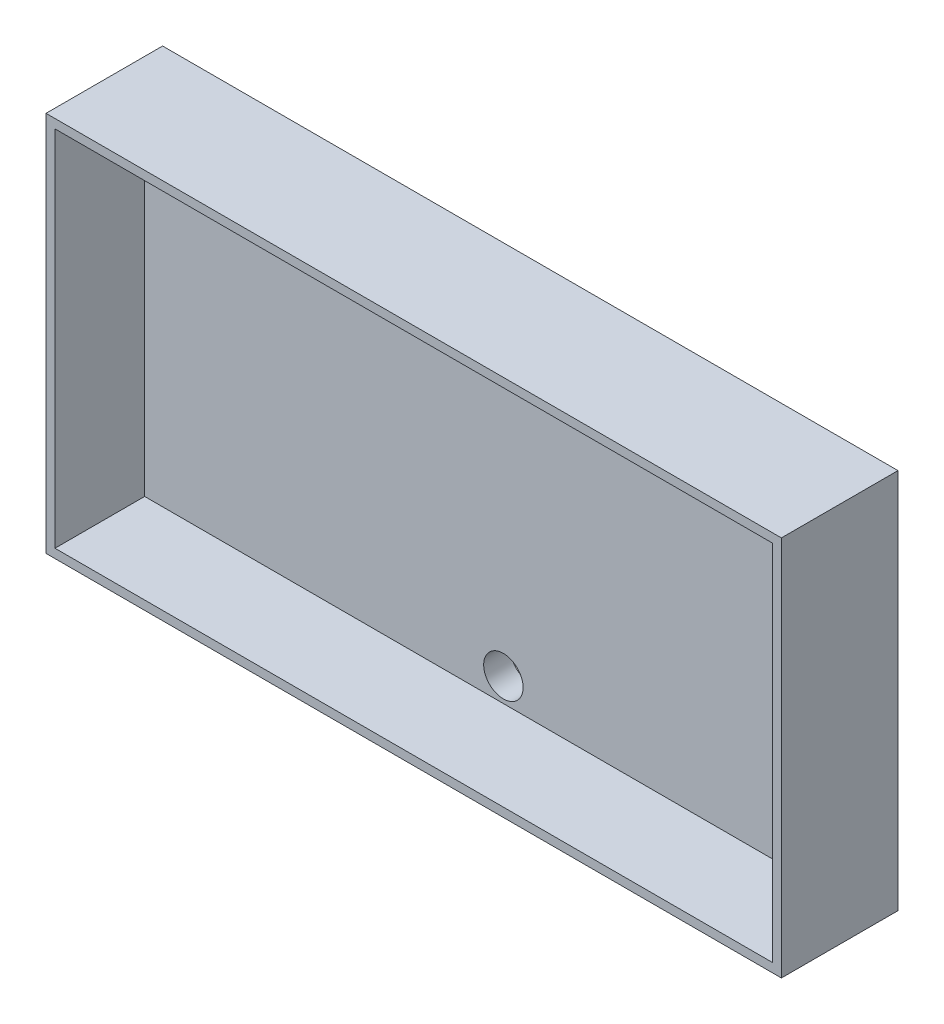
SolidWorks part; units mm, degrees
ref_plane "Front Plane" through (0, 0, 0) normal (0, 0, 1) x (1, 0, 0)
ref_plane "Top Plane" through (0, 0, 0) normal (0, 1, 0) x (1, 0, 0)
ref_plane "Right Plane" through (0, 0, 0) normal (1, 0, 0) x (0, 0, -1)
sketch "Sketch1" plane through (0, 0, 0) normal (0, 0, 1) x (1, 0, 0)
  line L0 (-1000, 0) -> (49000, 0) construction
  line L1 (-40, 20.25) -> (40, 20.25)
  line L2 (-40, 20.25) -> (-40, -20.25)
  line L3 (-40, -20.25) -> (40, -20.25)
  line L4 (40, 20.25) -> (40, -20.25)
  line L5 (0, -1000) -> (0, 49000) construction
  dimension "D1" = 80
  dimension "D2" = 40.5
extrude "Vysunout tenkostěnný1" add sketch "Sketch1" along normal blind 10 thin thin type one direction wall 1
sketch "Skica1" plane through (0, 0, 0) normal (0, 0, 1) x (1, 0, 0)
  line L0 (-41, -21.25) -> (41, -21.25) construction
  line L1 (-41, 21.25) -> (-41, -21.25) construction
  line L2 (41, -21.25) -> (41, 21.25) construction
  line L3 (41, 21.25) -> (-41, 21.25) construction
  line L4 (-41, -21.25) -> (41, -21.25)
  line L5 (-41, 21.25) -> (-41, -21.25)
  line L6 (41, -21.25) -> (41, 21.25)
  line L7 (41, 21.25) -> (-41, 21.25)
extrude "Přidat vysunutím1" add sketch "Skica1" against normal blind 3
sketch "Sketch3" plane through (0, 0, 0) normal (0, 0, 1) x (1, 0, 0)
  line L0 (-1000, 0) -> (49000, 0) construction
  circle A0 centre (0, -17.6) radius 2.2
  circle A1 centre (0, 17.6) radius 2.2
  dimension "D1" = 4.4
  dimension "D2" = 4.4
  dimension "D3" = 35.2
extrude "Cut-Extrude2" cut sketch "Sketch3" against normal through all both and the other way through all
